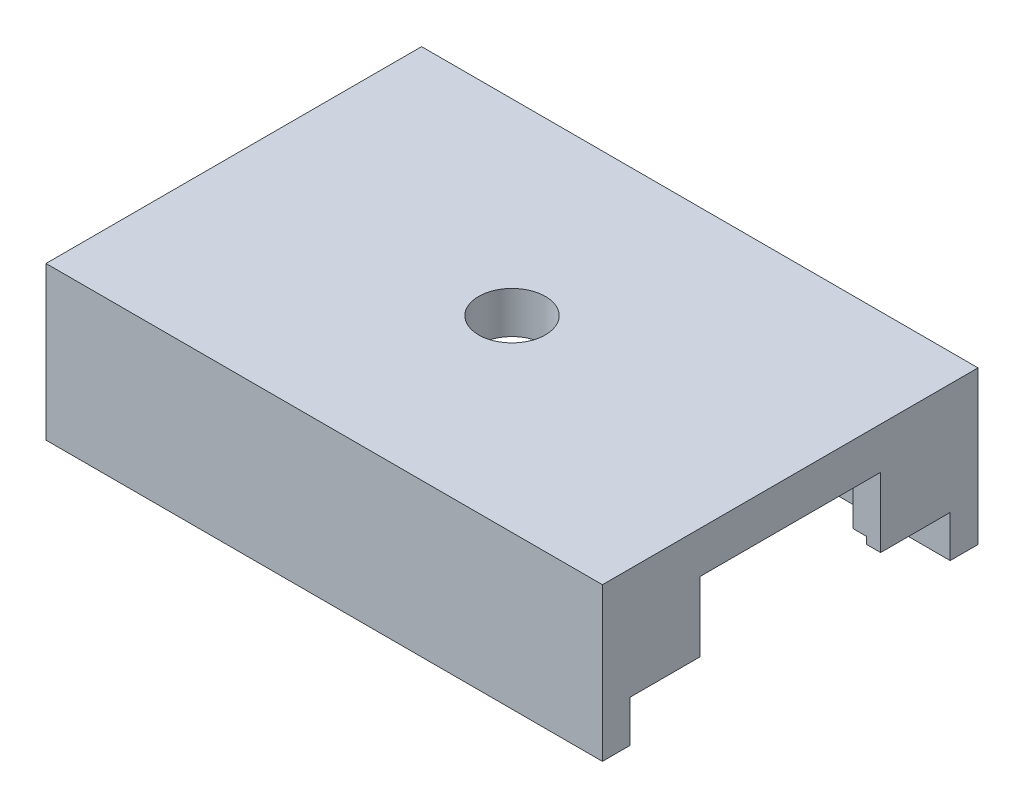
SolidWorks part; units mm, degrees
material "PLA"
ref_plane "Front Plane" through (0, 0, 0) normal (0, 0, 1) x (1, 0, 0)
ref_plane "Top Plane" through (0, 0, 0) normal (0, 1, 0) x (1, 0, 0)
ref_plane "Right Plane" through (0, 0, 0) normal (1, 0, 0) x (0, 0, -1)
sketch "Sketch1" plane through (0, 0, 0) normal (0, 1, 0) x (1, 0, 0)
  line L1 (-11.5, 11.5) -> (11.5, 11.5)
  line L2 (-11.5, 11.5) -> (-11.5, -11.5)
  line L3 (-11.5, -11.5) -> (11.5, -11.5)
  line L4 (11.5, 11.5) -> (11.5, -11.5)
  line L5 (-11.5, 11.5) -> (11.5, -11.5) construction
  line L6 (-11.5, -11.5) -> (11.5, 11.5) construction
  point P0 (0, 0)
  dimension "D1" = 23
  dimension "D2" = 23
sketch "Sketch2" plane through (0, 0, 0) normal (0, 1, 0) x (1, 0, 0)
  line L0 (-10.5, 8.3787) -> (-10.5, -8.3787)
  line L1 (-5, -5) -> (5, -5)
  line L3 (-5, 5) -> (5, 5)
  line L5 (-5, -5) -> (5, 5) construction
  line L6 (-5, 5) -> (5, -5) construction
  line L7 (10.5, 8.3787) -> (10.5, -8.3787)
  line L8 (-10.5, 8.3787) -> (-8.8713, 6.75)
  line L9 (-8.8713, 6.75) -> (-9.5, 6.75)
  line L10 (-9.5, -6.75) -> (-8.8713, -6.75)
  line L11 (-10.5, 8.3787) -> (8.3787, -10.5)
  line L12 (-8.8713, -6.75) -> (-10.5, -8.3787)
  line L13 (-8.3787, 10.5) -> (10.5, -8.3787)
  line L15 (-10.5, -8.3787) -> (8.3787, 10.5)
  line L17 (-8.3787, -10.5) -> (10.5, 8.3787)
  line L19 (-9.5, -6.75) -> (9.5, -6.75)
  line L20 (-9.5, -6.75) -> (-9.5, 6.75)
  line L21 (-9.5, 6.75) -> (9.5, 6.75)
  line L22 (9.5, -6.75) -> (9.5, 6.75)
  line L23 (-9.5, -6.75) -> (9.5, 6.75) construction
  line L24 (-9.5, 6.75) -> (9.5, -6.75) construction
  arc A2 (-5, -5) -> (-5, 5) centre (-1.2418, 0) cw
  arc A3 (5, 5) -> (5, -5) centre (1.2582, 0) cw
  point P0 (0, 0)
  point P12 (0, 0)
  point P22 (0, 0)
  point P25 (0, 0)
  point P28 (0, 0)
  point P33 (-1.0607, -1.0607)
  point P38 (1.0607, 1.0607)
  point P43 (-1.0607, 1.0607)
  point P46 (1.0607, -1.0607)
  dimension "D1" = 19
sketch "Sketch3" plane through (0, 0, 0) normal (0, 1, 0) x (1, 0, 0)
  line L3 (20, -20) -> (-20, -20)
  line L4 (20, -20) -> (20, 20)
  line L5 (20, 20) -> (-20, 20)
  line L6 (-20, -20) -> (-20, 20)
  line L7 (20, -20) -> (-20, 20) construction
  line L8 (20, 20) -> (-20, -20) construction
  circle A0 centre (0, 0) radius 5
  circle A1 centre (0, 0) radius 2.4
  point P7 (0, 0)
  point P8 (-11.5, 0)
extrude "Boss-Extrude2" add sketch "Sketch3" against normal blind 3 contours L6 L3 L4 L5 A0 | A0 A1
sketch "Sketch4" plane through (0, -3, 0) normal (0, -1, 0) x (1, 0, 0)
  line L0 (0, 11.5) -> (0, -11.5)
  line L1 (20, -11.5) -> (-20, -11.5)
  line L2 (20, -11.5) -> (20, -13.5)
  line L3 (-20, -11.5) -> (-20, -13.5)
  line L4 (20, -13.5) -> (-20, -13.5)
  line L5 (20, 20) -> (20, -20) construction
  line L6 (-20, 20) -> (-20, -20) construction
  line L7 (12.65, 0) -> (-12.65, 0) construction
  line L8 (-20, 11.5) -> (-20, 13.5)
  line L9 (20, 13.5) -> (-20, 13.5)
  line L10 (20, 11.5) -> (20, 13.5)
  line L11 (20, 11.5) -> (-20, 11.5)
  point P4 (0, 0)
  line M6 (-20, 20) -> (-20, -20)
  line M8 (20, -20) -> (20, 20)
extrude "Boss-Extrude3" add sketch "Sketch4" along normal blind 8 contours L4 L1 M8 M6 | L11 L9 M8 M6
sketch "Sketch5" plane through (0, 0, -11.5) normal (0, 0, 1) x (1, 0, 0)
  line L0 (0, -3) -> (0, -8)
  line L1 (20, -3) -> (-20, -3) construction
  line L2 (0, -8) -> (0, -9.5)
  line L3 (20, -11) -> (-20, -11) construction
  line L4 (5, -8) -> (-5, -8)
  line L5 (5, -8) -> (5, -11)
  line L6 (5, -11) -> (-5, -11)
  line L7 (-5, -8) -> (-5, -11)
  line L8 (5, -8) -> (-5, -11) construction
  line L9 (5, -11) -> (-5, -8) construction
  line L13 (19, -7.5) -> (-19, -7.5)
  line L14 (19, -7.5) -> (19, -8.5)
  line L15 (19, -8.5) -> (-19, -8.5)
  line L16 (-19, -7.5) -> (-19, -8.5)
  line L17 (19, -7.5) -> (-19, -8.5) construction
  line L18 (19, -8.5) -> (-19, -7.5) construction
  dimension "D1" = 10
  dimension "D2" = 1
sketch "Sketch6" plane through (0, -3, 0) normal (0, -1, 0) x (1, 0, 0)
  line L1 (20, 11.5) -> (18, 11.5)
  line L2 (20, 11.5) -> (20, 6.5)
  line L3 (20, 6.5) -> (18, 6.5)
  line L4 (18, 11.5) -> (18, 6.5)
  line L5 (12.65, 0) -> (-12.65, 0) construction
  line L6 (20, -6.5) -> (18, -6.5)
  line L7 (18, -11.5) -> (18, -6.5)
  line L8 (20, -11.5) -> (18, -11.5)
  line L9 (20, -11.5) -> (20, -6.5)
  line L10 (0, -12.65) -> (0, 12.65) construction
  line L11 (-20, -11.5) -> (-20, -6.5)
  line L12 (-20, -11.5) -> (-18, -11.5)
  line L13 (-18, -11.5) -> (-18, -6.5)
  line L14 (-20, -6.5) -> (-18, -6.5)
  line L15 (-20, 6.5) -> (-18, 6.5)
  line L16 (-18, 11.5) -> (-18, 6.5)
  line L17 (-20, 11.5) -> (-18, 11.5)
  line L18 (-20, 11.5) -> (-20, 6.5)
extrude "Boss-Extrude5" add sketch "Sketch6" along normal blind 5
sketch "Sketch7" plane through (0, -3, 0) normal (0, -1, 0) x (-1, 0, 0)
  line L1 (-20, -13.5) -> (20, -13.5)
  line L2 (-20, -13.5) -> (-20, -20)
  line L3 (-20, -20) -> (20, -20)
  line L4 (20, -13.5) -> (20, -20)
extrude "Cut-Extrude1" cut sketch "Sketch7" against normal blind 3
sketch "Sketch8" plane through (0, -3, 0) normal (0, -1, 0) x (1, 0, 0)
  line L1 (20, -13.5) -> (-20, -13.5)
  line L2 (20, -13.5) -> (20, -20)
  line L3 (20, -20) -> (-20, -20)
  line L4 (-20, -13.5) -> (-20, -20)
extrude "Cut-Extrude2" cut sketch "Sketch8" against normal blind 3
extrude "Cut-Extrude3" cut sketch "Sketch5" against normal blind 1 and the other way up to next contours L15 L14 L13 L0 L4 L5 | L13 L16 L15 L7 L4 L0 | L15 L2 L4 L7 | L15 L5 L4 L2
mirror "Mirror2" about plane through (0, 0, 0) normal (0, 0, 1) of "Cut-Extrude3"
